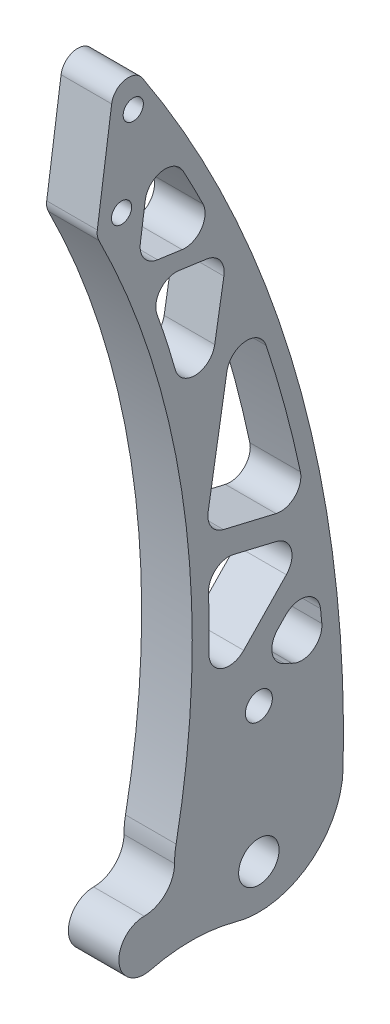
SolidWorks part; units mm, degrees
material "6061-T6 (SS)"
ref_plane "Front Plane" through (0, 0, 0) normal (0, 0, 1) x (1, 0, 0)
ref_plane "Top Plane" through (0, 0, 0) normal (0, 1, 0) x (1, 0, 0)
ref_plane "Right Plane" through (0, 0, 0) normal (1, 0, 0) x (0, 0, -1)
sketch "Sketch1" plane through (0, 0, 0) normal (1, 0, 0) x (0, 0, -1)
  line L0 (0, 0) -> (0, 200) construction
  line L1 (0, 0) -> (-44.9902, 194.874) construction
  line L2 (-41.8588, 217.155) -> (-48.1216, 172.593)
  circle A0 centre (0, -12) radius 6
  circle A1 centre (0, 0) radius 25
  arc A2 (24.9928, -0.6007) -> (-41.8588, 217.155) centre (-334.9033, 8.0499) ccw
  arc A3 (-24.539, 4.7789) -> (-48.1216, 172.593) centre (-279.7445, 54.4794) ccw
  dimension "D2" = 12
  dimension "D3" = 50
  dimension "D5" = 360
  dimension "D6" = 260
  dimension "D1" = 200
  dimension "D4" = 13
  dimension "D7" = 45
  dimension "D8" = 8
  dimension "D9" = 12
extrude "Boss-Extrude1" add sketch "Sketch1" along normal blind 15
sketch "Sketch2" plane through (15, 0, 0) normal (1, 0, 0) x (0, 0, -1)
  line L0 (0, -12) -> (0, 208) construction
  circle A0 centre (0, 28) radius 4
  dimension "D3" = 8
  dimension "D2" = 40
  dimension "D1" = 220
extrude "Cut-Extrude1" cut sketch "Sketch2" against normal through all
sketch "Sketch3" plane through (15, 0, 0) normal (1, 0, 0) x (0, 0, -1)
  line L0 (-30.6472, 246.6326) -> (-44.1841, 150.313) construction
  line L1 (-41.8588, 217.155) -> (-48.1216, 172.593) construction
  circle A0 centre (-40.7145, 175) radius 3
  circle A1 centre (-37.2352, 199.7567) radius 3
  dimension "D2" = 6
  dimension "D1" = 25
  dimension "D3" = 7
  dimension "D4" = 175
extrude "Cut-Extrude2" cut sketch "Sketch3" against normal through all
sketch "Sketch4" plane through (15, 0, 0) normal (1, 0, 0) x (0, 0, -1)
  line L0 (-31.2609, 191.9692) -> (-35.9768, 158.4135)
  line L1 (-41.8588, 217.155) -> (-48.1216, 172.593) construction
  line L2 (-35.9768, 158.4135) -> (-11.7498, 155.0086)
  line L3 (-33.7602, 153.0529) -> (-9.3543, 149.6228)
  line L4 (-9.3543, 149.6228) -> (-18.1663, 96.9275)
  line L5 (-5.7303, 140.9792) -> (-15.9585, 79.8154)
  line L6 (-15.9585, 79.8154) -> (14.1619, 72.6915)
  line L7 (15.4681, 65.1894) -> (-15.3566, 72.4799)
  line L8 (15.4681, 65.1894) -> (-15.6193, 32.9646)
  line L10 (-2, 37) -> (16.7796, 56.4667)
  arc A2 (-19.6312, 3.8231) -> (-43.6673, 174.8644) centre (-279.7445, 54.4794) ccw
  arc A3 (-15.6193, 32.9646) -> (-35.9768, 158.4135) centre (-279.7445, 54.4794) ccw
  arc A4 (-15.6193, 32.9646) -> (19.7211, 24.3772) centre (-2, 12) cw
  arc A5 (19.9942, -0.4806) -> (-45.9289, 214.2508) centre (-334.9033, 8.0499) ccw
  arc A6 (19.7211, 24.3772) -> (-31.2609, 191.9692) centre (-334.9033, 8.0499) ccw
  dimension "D3" = 25
  dimension "D4" = 12
  dimension "D5" = 2
  dimension "D6" = 14
  dimension "D7" = 5
  dimension "D8" = 5
  dimension "D9" = 7
  dimension "D10" = 7
  dimension "D1" = 5
  dimension "D2" = 5
extrude "Cut-Extrude3" cut sketch "Sketch4" against normal through all contours L2 A6 L0 | A3 L4 L3 | L6 A6 L5 | A3 L8 L7 | A4 A6 L10
fillet "Fillet1" radius 6 15 edges at (7.5, 191.9692, 31.2609) (7.5, 155.0086, 11.7498) (7.5, 158.4135, 35.9768) (7.5, 153.0529, 33.7602) (7.5, 149.6228, 9.3543) (7.5, 96.9275, 18.1663) (7.5, 140.9792, 5.7303) (7.5, 72.6915, -14.1619) (7.5, 79.8154, 15.9585) (7.5, 72.4799, 15.3566) (7.5, 65.1894, -15.4681) (7.5, 32.9646, 15.6193) (7.5, 56.4667, -16.7796) (7.5, 37, 2) (7.5, 24.3772, -19.7211)
sketch "Sketch5" plane through (15, 0, 0) normal (1, 0, 0) x (0, 0, -1)
  circle A0 centre (-34, -16.5) radius 7.5
  arc A3 (-25, 0) -> (-34, -9) centre (-34, 0) cw
  arc A4 (-32.1775, -23.7752) -> (-6.6759, -24.0922) centre (-20.0276, -72.2765) cw
  arc A5 (-24.539, 4.7789) -> (24.9928, -0.6007) centre (0, 0) ccw construction
  dimension "D1" = 15
  dimension "D2" = 50
  dimension "D3" = 9
  dimension "D4" = 34
extrude "Boss-Extrude2" add sketch "Sketch5" against normal up to surface (15 mm away)
fillet "Fillet2" radius 5 2 edges at (7.5, 172.593, 48.1216) (7.5, 217.155, 41.8588)
sketch "Sketch6" plane through (15, 0, 0) normal (1, 0, 0) x (0, 0, -1)
  line L1 (-67.6782, 214.7113) -> (52.3218, 214.7113)
  line L2 (-67.6782, 214.7113) -> (-67.6782, -35.2887)
  line L3 (-67.6782, -35.2887) -> (52.3218, -35.2887)
  line L4 (52.3218, 214.7113) -> (52.3218, -35.2887)
  dimension "D1" = 250
  dimension "D2" = 120
